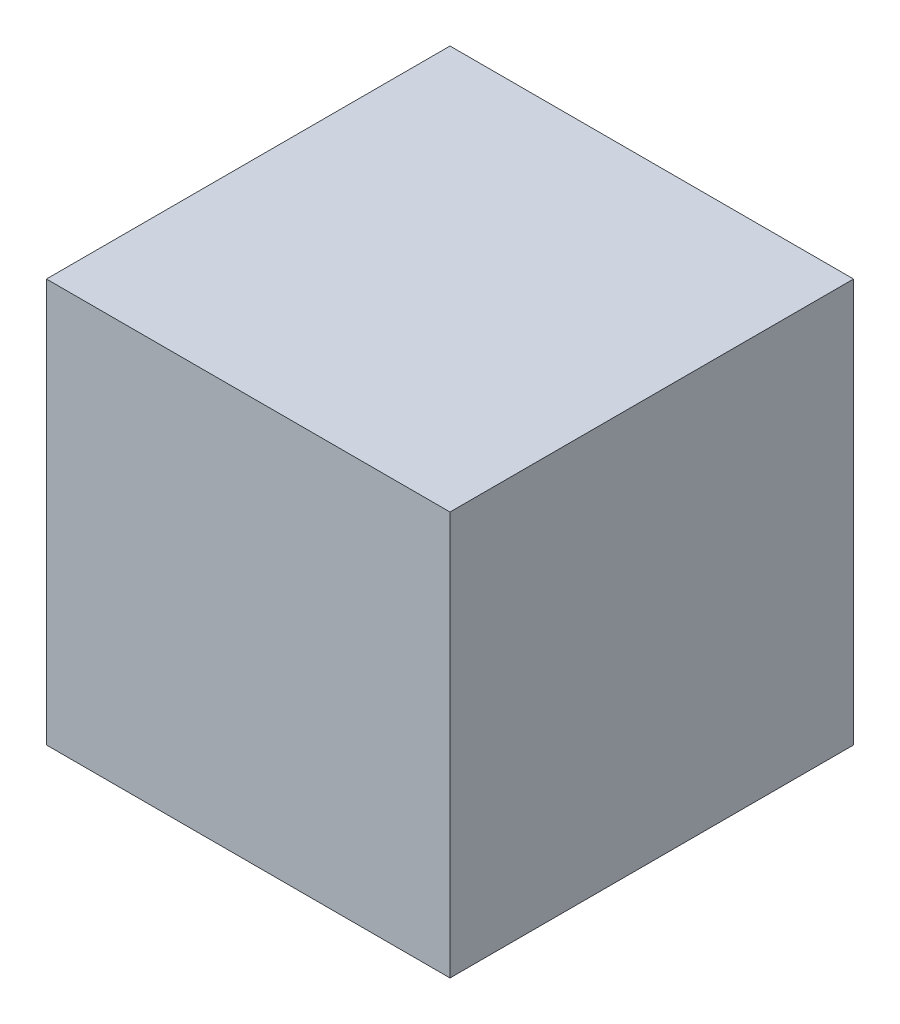
SolidWorks part; units mm, degrees
ref_plane "Ebene1" through (0, 0, 0) normal (0, 0, 1) x (1, 0, 0)
ref_plane "Ebene2" through (0, 0, 0) normal (0, 1, 0) x (1, 0, 0)
ref_plane "Ebene3" through (0, 0, 0) normal (1, 0, 0) x (0, 0, -1)
sketch "Skizze1" plane through (0, 0, 0) normal (0, 0, 1) x (1, 0, 0)
  line L1 (0, 0) -> (100, 0)
  line L2 (0, 0) -> (0, 100)
  line L3 (0, 100) -> (100, 100)
  line L4 (100, 0) -> (100, 100)
  dimension "D1" = 100
  dimension "D2" = 100
extrude "Aufsatz-Linear austragen1" add sketch "Skizze1" along normal blind 100
